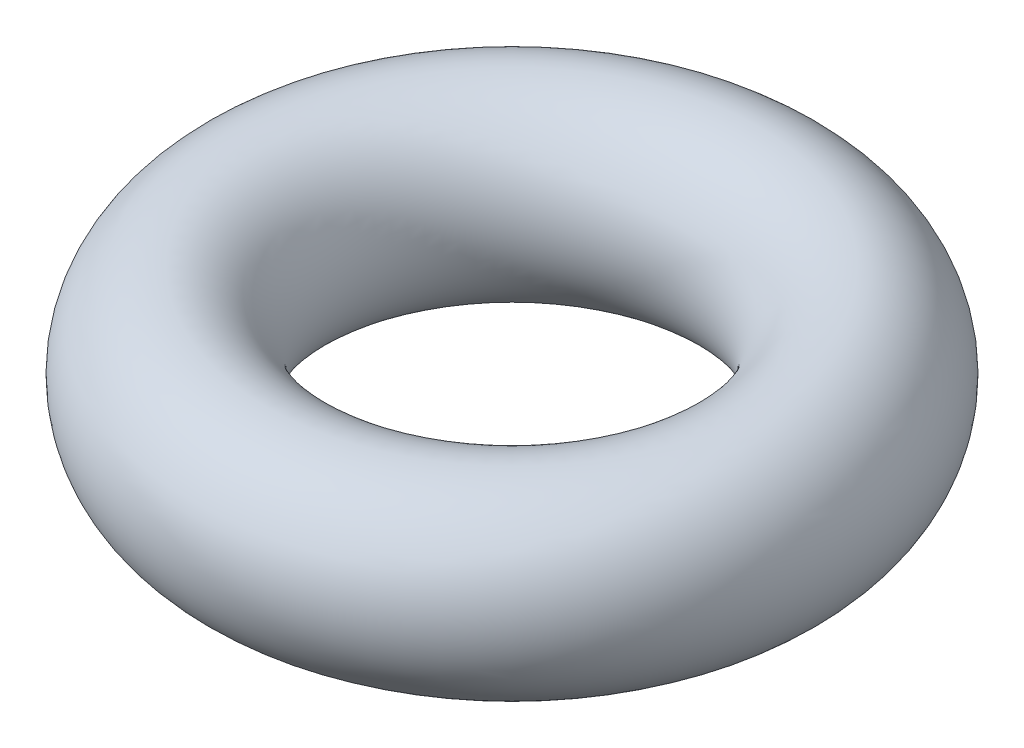
SolidWorks part; units mm, degrees
material "Rubber"
ref_plane "Front Plane" through (0, 0, 0) normal (0, 0, 1) x (1, 0, 0)
ref_plane "Top Plane" through (0, 0, 0) normal (0, 1, 0) x (1, 0, 0)
ref_plane "Right Plane" through (0, 0, 0) normal (1, 0, 0) x (0, 0, -1)
sketch "body_sketch" plane through (0, 0, 0) normal (0, 0, 1) x (1, 0, 0)
  line L0 (-2.3, 0) -> (0, 0) construction
  line L1 (-2.3, 0.875) -> (0, 0.875) construction
  line L2 (-2.3, -0.875) -> (0, -0.875) construction
  line L3 (0, 0.875) -> (0, -0.875) construction
  ellipse E0 centre (-2.3, 0) end of major axis (-2.3, 0.875) minor radius 0.8
  dimension "D1" = 1.5
  dimension "D3" = 3.1
  dimension "D4" = 1.75
ref_axis "axis" through (0, 0, 0) along (0, 1, 0)
revolve "body" add sketch "body_sketch" angle 360 about axis through (0, 0, 0) along (0, 1, 0)
ref_plane "top_plane" through (0, 0.875, 0) normal (0, 1, 0) x (1, 0, 0)
ref_plane "bottom_plane" through (0, -0.875, 0) normal (0, 1, 0) x (1, 0, 0)
